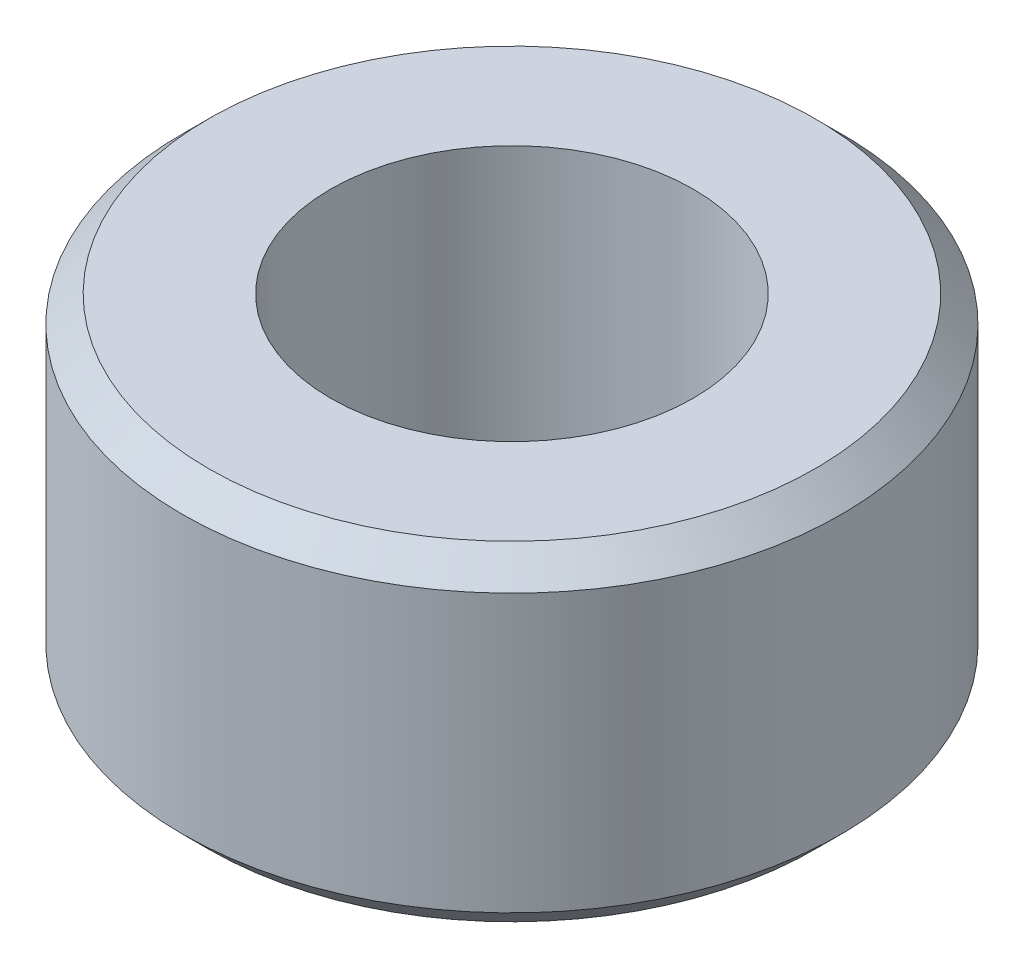
SolidWorks part; units mm, degrees
material "ABS"
ref_plane "Front Plane" through (0, 0, 0) normal (0, 0, 1) x (1, 0, 0)
ref_plane "Top Plane" through (0, 0, 0) normal (0, 1, 0) x (1, 0, 0)
ref_plane "Right Plane" through (0, 0, 0) normal (1, 0, 0) x (0, 0, -1)
sketch "Sketch1" plane through (0, 0, 0) normal (0, 1, 0) x (1, 0, 0)
  circle A0 centre (0, 0) radius 2.75
  circle A1 centre (0, 0) radius 5
  dimension "D1" = 5.5
  dimension "D2" = 10
extrude "Boss-Extrude1" add sketch "Sketch1" along normal mid plane 5
chamfer "Chamfer1" distance 0.4 angle 45 2 edges at (0, -2.5, 5) (0, 2.5, 5)
